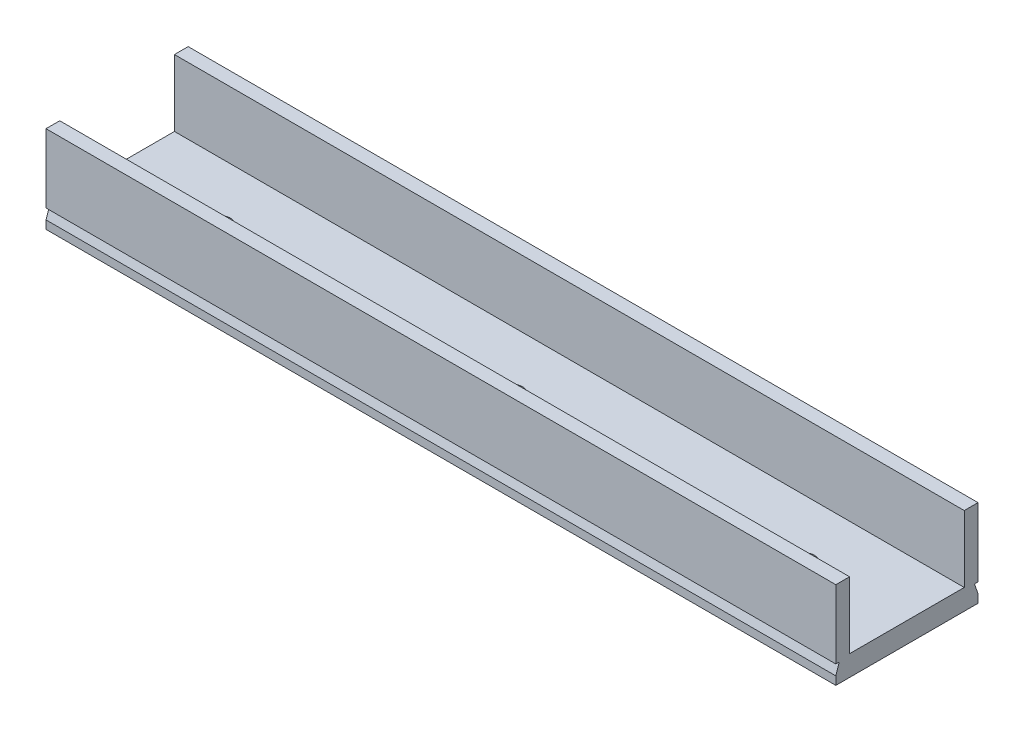
SolidWorks part; units mm, degrees
ref_plane "Front Plane" through (0, 0, 0) normal (0, 0, 1) x (1, 0, 0)
ref_plane "Top Plane" through (0, 0, 0) normal (0, 1, 0) x (1, 0, 0)
ref_plane "Right Plane" through (0, 0, 0) normal (1, 0, 0) x (0, 0, -1)
sketch "Croquis1" plane through (0, 0, 0) normal (0, 1, 0) x (1, 0, 0)
  line L0 (-57.5, -12.5) -> (-57.5, 12.5)
  line L1 (-57.5, -12.5) -> (57.5, -12.5)
  line L2 (-57.5, 12.5) -> (57.5, 12.5)
  line L3 (57.5, -12.5) -> (57.5, 12.5)
  line L4 (-57.5, -12.5) -> (57.5, 12.5) construction
  line L5 (-57.5, 12.5) -> (57.5, -12.5) construction
  line L6 (71, -10.35) -> (71, 10.35)
  line L7 (71, -10.35) -> (-71, -10.35)
  line L8 (71, 10.35) -> (-71, 10.35)
  line L9 (-71, -10.35) -> (-71, 10.35)
  line L10 (71, -10.35) -> (-71, 10.35) construction
  line L11 (71, 10.35) -> (-71, -10.35) construction
  point P1 (0, 0)
  point P2 (0, 0)
  dimension "D1" = 115
  dimension "D2" = 25
  dimension "D3" = 142
  dimension "D4" = 2.15
extrude "Saliente-Extruir2" add sketch "Croquis1" along normal blind 3 contours L3 L8 L0 L7
sketch "Croquis6" plane through (0, 3, 0) normal (0, 1, 0) x (1, 0, 0)
  line L0 (0, 0) -> (0, 6.8298) construction
  line L1 (-57.5, -10.35) -> (-57.5, 10.35) construction
  circle A0 centre (-42.5, 0) radius 1.5
  circle A1 centre (0, 0) radius 1.5
  circle A2 centre (42.5, 0) radius 1.5
  point P9 (-57.5, 0)
  dimension "D1" = 3
  dimension "D2" = 3
  dimension "D3" = 15
extrude "Cortar-Extruir4" cut sketch "Croquis6" against normal blind 3
sketch "Croquis7" plane through (0, 3, 0) normal (0, 1, 0) x (1, 0, 0)
  line L0 (-57.5, 8.35) -> (-57.5, 10.35)
  line L1 (-57.5, -10.35) -> (-57.5, 10.35) construction
  line L2 (-57.5, 10.35) -> (57.5, 10.35)
  line L3 (57.5, -10.35) -> (57.5, 10.35) construction
  line L4 (57.5, 10.35) -> (-57.5, 10.35) construction
  line L5 (57.5, 10.35) -> (57.5, 8.35)
  line L6 (57.5, 8.35) -> (-57.5, 8.35)
  line L7 (0, 0) -> (-103.6833, 0) construction
  line L8 (57.5, -8.35) -> (-57.5, -8.35)
  line L9 (57.5, -10.35) -> (57.5, -8.35)
  line L10 (-57.5, -10.35) -> (57.5, -10.35)
  line L11 (-57.5, -8.35) -> (-57.5, -10.35)
  dimension "D1" = 2
extrude "Saliente-Extruir3" add sketch "Croquis7" along normal blind 9.7
sketch "Croquis9" plane through (-57.5, 0, 0) normal (-1, 0, 0) x (0, 0, 1)
  line L1 (-10.35, 2.7) -> (-9.85, 2.7)
  line L2 (-10.35, 12.7) -> (-10.35, 0) construction
  line L3 (-9.85, 2.7) -> (-10.35, 1.2)
  line L4 (-10.35, 1.2) -> (-10.35, 2.7)
  line L5 (-10.35, 12.7) -> (-8.35, 12.7) construction
  line L6 (0, 0) -> (0, 4.8094) construction
  line L7 (10.35, 0) -> (-10.35, 0) construction
  line L8 (10.35, 2.7) -> (9.85, 2.7)
  line L9 (10.35, 1.2) -> (10.35, 2.7)
  line L10 (9.85, 2.7) -> (10.35, 1.2)
  dimension "D1" = 10
  dimension "D2" = 1.5
  dimension "D3" = 0.5
extrude "Cortar-Extruir5" cut sketch "Croquis9" against normal blind 224
